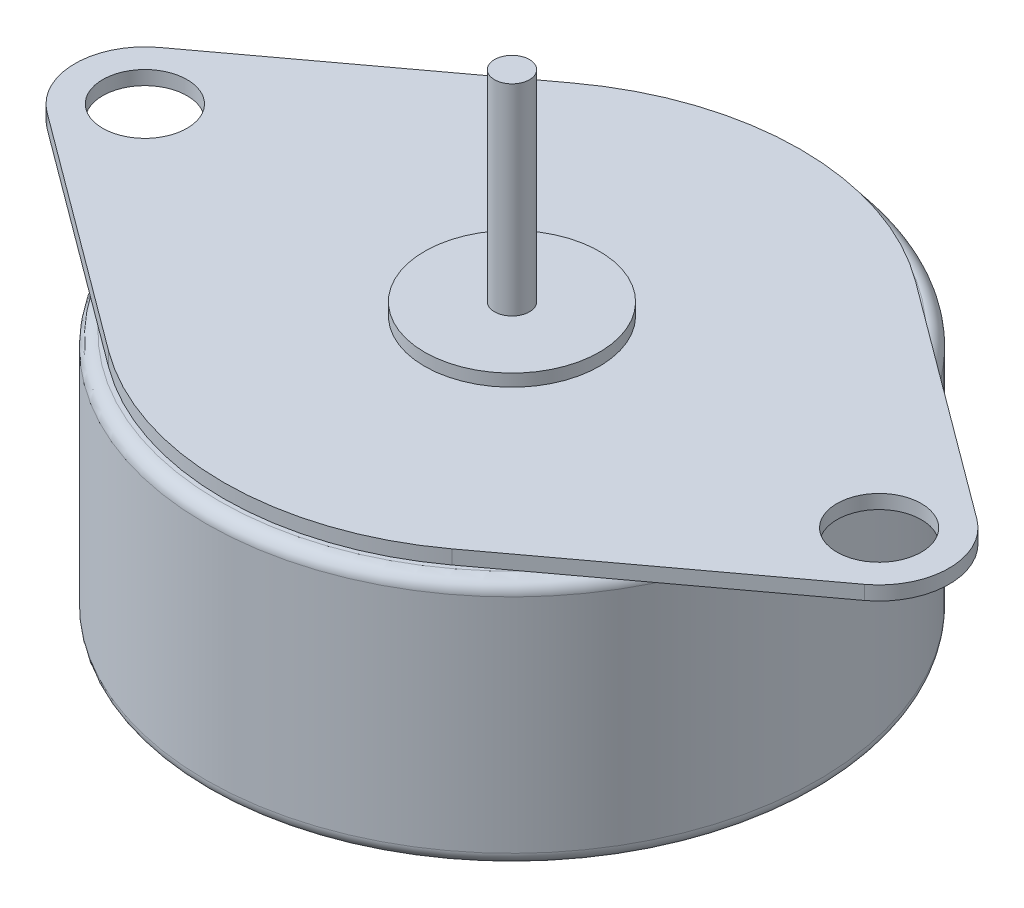
SolidWorks part; units mm, degrees
ref_plane "Front Plane" through (0, 0, 0) normal (0, 0, 1) x (1, 0, 0)
ref_plane "Top Plane" through (0, 0, 0) normal (0, 1, 0) x (1, 0, 0)
ref_plane "Right Plane" through (0, 0, 0) normal (1, 0, 0) x (0, 0, -1)
sketch "Sketch1" plane through (0, 0, 0) normal (0, 1, 0) x (1, 0, 0)
  circle A0 centre (0, 0) radius 17.5
  dimension "D1" = 35
extrude "Extrude1" add sketch "Sketch1" along normal blind 14.2
fillet "Fillet1" radius 0.75 2 edges at (0, 0, 17.5) (0, 14.2, 17.5)
sketch "Sketch2" plane through (0, 14.2, 0) normal (0, 1, 0) x (-1, 0, 0)
  line L0 (0, -13.8389) -> (0, 0) construction
  line L1 (0, 0) -> (21, 0) construction
  line L2 (23.381, -3.2142) -> (9.8214, -13.2586)
  line L3 (23.381, 3.2142) -> (9.8214, 13.2586)
  line L4 (-23.381, -3.2142) -> (-9.8214, -13.2586)
  line L5 (-23.381, 3.2142) -> (-9.8214, 13.2586)
  arc A0 (-9.8214, -13.2586) -> (9.8214, -13.2586) centre (0, 0) ccw
  circle A1 centre (21, 0) radius 2.413
  circle A2 centre (-21, 0) radius 2.413
  arc A3 (23.381, -3.2142) -> (23.381, 3.2142) centre (21, 0) ccw
  arc A4 (-23.381, -3.2142) -> (-23.381, 3.2142) centre (-21, 0) cw
  arc A5 (9.8214, 13.2586) -> (-9.8214, 13.2586) centre (0, 0) ccw
  dimension "D1" = 50
  dimension "D2" = 42
  dimension "D3" = 4.826
  dimension "D4" = 16.5
extrude "Extrude2" add sketch "Sketch2" along normal blind 0.8
sketch "Sketch3" plane through (0, 0, 0) normal (0, -1, 0) x (1, 0, 0)
  circle A0 centre (0, 0) radius 5
  dimension "D1" = 10
extrude "Extrude3" add sketch "Sketch3" along normal blind 2
sketch "Sketch4" plane through (0, 15, 0) normal (0, 1, 0) x (-1, 0, 0)
  circle A0 centre (0, 0) radius 5
  dimension "D1" = 10
extrude "Extrude4" add sketch "Sketch4" along normal blind 0.7
sketch "Sketch5" plane through (0, 15.7, 0) normal (0, 1, 0) x (-1, 0, 0)
  circle A0 centre (0, 0) radius 1
  dimension "D1" = 2
extrude "Extrude5" add sketch "Sketch5" along normal blind 11.5
